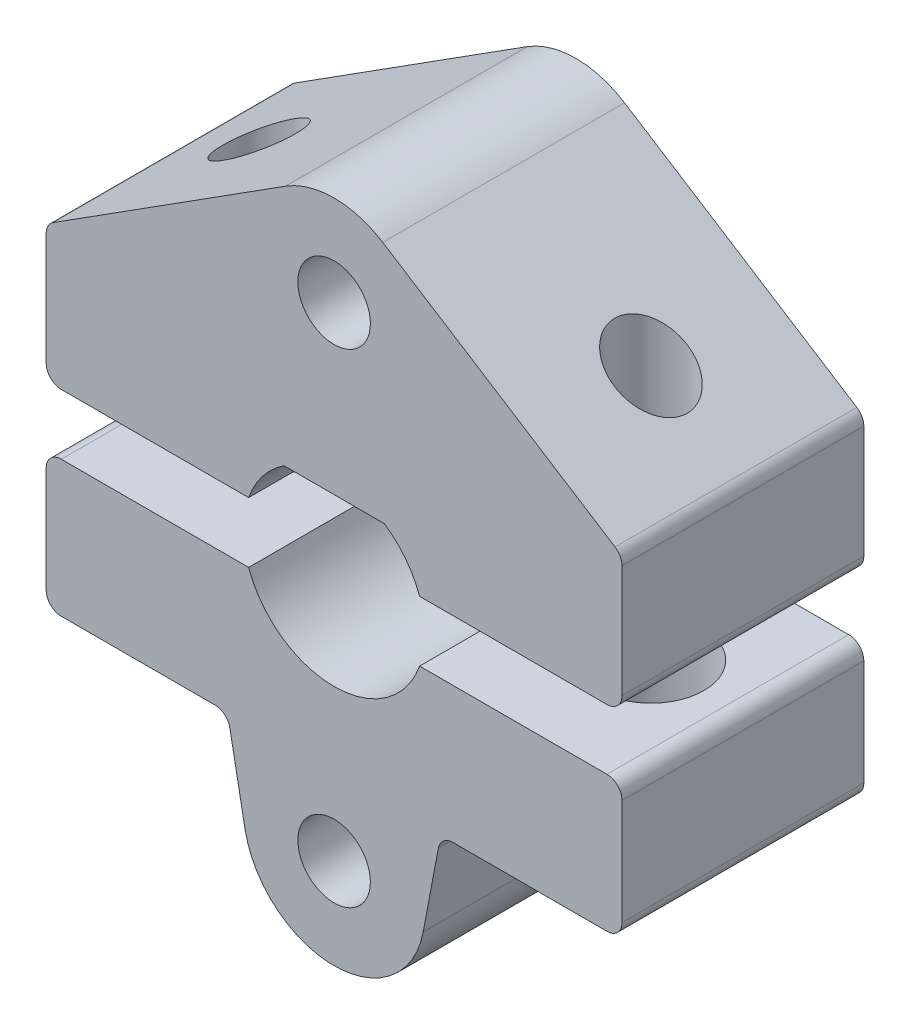
SolidWorks part; units mm, degrees
material "6061-T6 (SS)"
ref_plane "前视基准面" through (0, 0, 0) normal (0, 0, 1) x (1, 0, 0)
ref_plane "上视基准面" through (0, 0, 0) normal (0, 1, 0) x (1, 0, 0)
ref_plane "右视基准面" through (0, 0, 0) normal (1, 0, 0) x (0, 0, -1)
sketch "草图1" plane through (0, 0, 0) normal (0, 0, 1) x (1, 0, 0)
  line L0 (-1.6583, 2.5) -> (1.6583, 2.5)
  line L1 (-9.2945, 5.6473) -> (-1.6092, 10.5319)
  line L2 (1.6092, 10.5319) -> (9.2945, 5.6473)
  line L3 (-9.5263, 5.2253) -> (-9.5263, 1.5)
  line L4 (-9.0263, 1) -> (-2.8284, 1)
  line L5 (9.5263, 1.5) -> (9.5263, 5.2253)
  line L6 (0, 1) -> (0, 0) construction
  line L7 (-9.0263, -1) -> (-2.8284, -1)
  line L8 (9.5263, -1.5) -> (9.5263, -5)
  line L9 (9.0263, -5.5) -> (3.9405, -5.5)
  line L10 (3.4493, -5.907) -> (2.9477, -8.5578)
  line L11 (-2.9477, -8.5578) -> (-3.4493, -5.907)
  line L12 (-3.9405, -5.5) -> (-9.0263, -5.5)
  line L13 (-9.5263, -5) -> (-9.5263, -1.5)
  line L14 (0, 0) -> (0, -1) construction
  line L15 (2.8284, 1) -> (9.0263, 1)
  line L16 (2.8284, -1) -> (9.0263, -1)
  line L17 (9.2945, 5.6473) -> (9.5263, 5.5) construction
  line L18 (9.5263, 5.5) -> (9.5263, 5.2253) construction
  arc A0 (-1.6583, 2.5) -> (-2.8284, 1) centre (0, 0) ccw
  circle A1 centre (0, 0) radius 8 construction
  circle A2 centre (0, 8) radius 1.2
  circle A3 centre (0, -8) radius 1.2
  arc A4 (-1.6092, 10.5319) -> (1.6092, 10.5319) centre (0, 8) cw
  circle A5 centre (0, 0) radius 11 construction
  arc A6 (2.9477, -8.5578) -> (-2.9477, -8.5578) centre (0, -8) cw
  arc A7 (-9.5263, 1.5) -> (-9.0263, 1) centre (-9.0263, 1.5) ccw
  arc A8 (-9.2945, 5.6473) -> (-9.5263, 5.2253) centre (-9.0263, 5.2253) ccw
  arc A9 (9.2945, 5.6473) -> (9.5263, 5.2253) centre (9.0263, 5.2253) cw
  arc A10 (9.0263, 1) -> (9.5263, 1.5) centre (9.0263, 1.5) ccw
  arc A11 (-9.0263, -5.5) -> (-9.5263, -5) centre (-9.0263, -5) cw
  arc A12 (-9.0263, -1) -> (-9.5263, -1.5) centre (-9.0263, -1.5) ccw
  arc A13 (9.5263, -5) -> (9.0263, -5.5) centre (9.0263, -5) cw
  arc A14 (9.0263, -1) -> (9.5263, -1.5) centre (9.0263, -1.5) cw
  arc A15 (3.9405, -5.5) -> (3.4493, -5.907) centre (3.9405, -6) ccw
  arc A16 (-3.4493, -5.907) -> (-3.9405, -5.5) centre (-3.9405, -6) ccw
  arc A17 (-2.8284, -1) -> (2.8284, -1) centre (0, 0) ccw
  arc A18 (2.8284, 1) -> (1.6583, 2.5) centre (0, 0) ccw
  point P31 (-9.5263, 1)
  point P34 (-9.5263, 5.5)
  point P39 (9.5263, 1)
  point P42 (-9.5263, -5.5)
  point P47 (9.5263, -5.5)
  point P52 (3.5263, -5.5)
  dimension "D1" = 16
  dimension "D2" = 6
  dimension "D4" = 2.4
  dimension "D6" = 22
  dimension "D10" = 0.5
  dimension "D5" = 4.5
  dimension "D3" = 2.5
  dimension "D7" = 1
  dimension "D9" = 6
extrude "凸台-拉伸1" add sketch "草图1" along normal blind 8
cosmetic thread "装饰螺纹线3" parameters "D2"=3
cosmetic thread "装饰螺纹线4" parameters "D2"=3
sketch "草图2" plane through (0, -5.5, 0) normal (0, -1, 0) x (1, 0, 0)
  line L0 (-9.5263, 4) -> (-6.4834, 4) construction
  line L1 (-9.5263, 8) -> (-9.5263, 0) construction
  line L2 (-6.4834, 4) -> (6.4834, 4) construction
  line L3 (6.4834, 4) -> (9.5263, 4) construction
  line L4 (9.5263, 8) -> (9.5263, 0) construction
  line L5 (6.4834, 8) -> (6.4834, 4) construction
  line L6 (3.9405, 8) -> (9.0263, 8) construction
  circle A0 centre (6.4834, 4) radius 1.2
  circle A1 centre (-6.4834, 4) radius 1.2
  dimension "D1" = 2.4
extrude "切除-拉伸1" cut sketch "草图2" against normal through all
cosmetic thread "装饰螺纹线1" parameters "D2"=3
cosmetic thread "装饰螺纹线2" parameters "D2"=3
sketch "草图3" plane through (0, -5.5, 0) normal (0, -1, 0) x (1, 0, 0)
  circle A0 centre (-6.4834, 4) radius 1.75
  circle A1 centre (6.4834, 4) radius 1.75
  dimension "D1" = 3.5
extrude "切除-拉伸2" cut sketch "草图3" against normal up to surface (4.5 mm away) up to face at (-5.2834, -1, 4)
